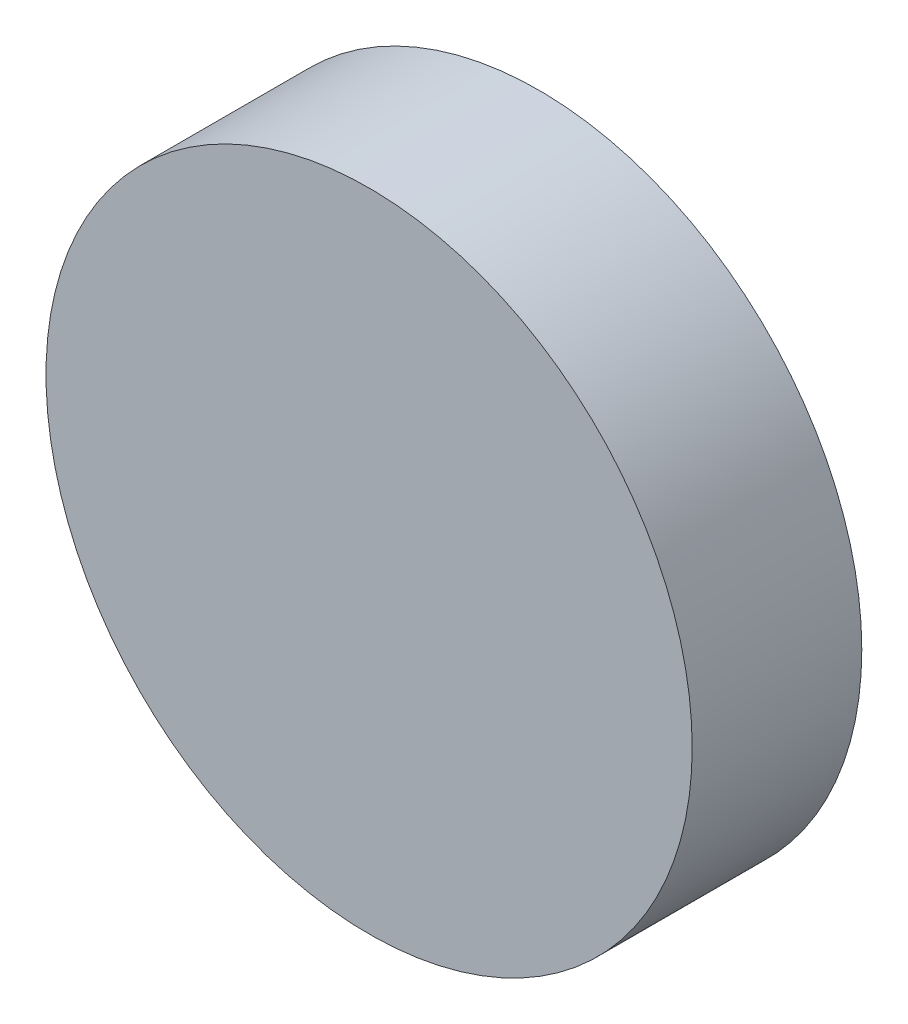
SolidWorks part; units mm, degrees
ref_plane "前视基准面" through (0, 0, 0) normal (0, 0, 1) x (1, 0, 0)
ref_plane "上视基准面" through (0, 0, 0) normal (0, 1, 0) x (1, 0, 0)
ref_plane "右视基准面" through (0, 0, 0) normal (1, 0, 0) x (0, 0, -1)
sketch "草图1" plane through (0, 0, 0) normal (0, 0, 1) x (1, 0, 0)
  circle A0 centre (0, 0) radius 19.05
  dimension "D1" = 38.1
extrude "凸台-拉伸1" add sketch "草图1" along normal blind 10
